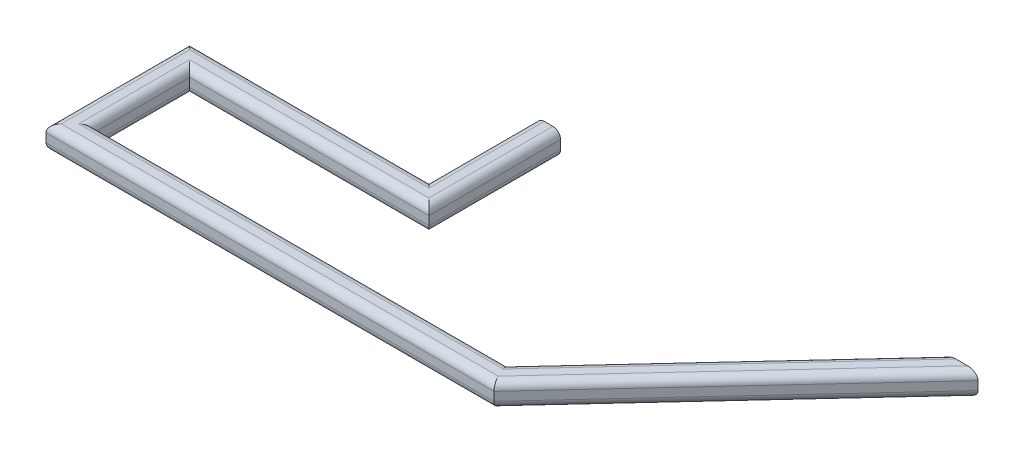
SolidWorks part; units mm, degrees
ref_plane "Front Plane" through (0, 0, 0) normal (0, 0, 1) x (1, 0, 0)
ref_plane "Top Plane" through (0, 0, 0) normal (0, 1, 0) x (1, 0, 0)
ref_plane "Right Plane" through (0, 0, 0) normal (1, 0, 0) x (0, 0, -1)
sketch "Sketch2" plane through (0, 0, 0) normal (0, 1, 0) x (1, 0, 0)
  line L1 (0, 0) -> (200, 0)
  line L2 (200, 0) -> (431.5, 250)
  line L3 (431.5, 250) -> (439.993, 259.1717)
  line L4 (439.993, 259.1717) -> (448.8318, 250.3328) construction
  line L5 (448.8318, 250.3328) -> (431.1541, 268.0105) construction
  line L6 (0, 125) -> (-250, 125)
  line L7 (-250, 125) -> (-250, 0)
  line L8 (-250, 0) -> (0, 0)
  line L9 (0, 250) -> (0, 125)
  point P4 (439.993, 259.1717)
  dimension "D1" = 250
  dimension "D2" = 431.5
  dimension "D3" = 200
  dimension "D4" = 12.5
  dimension "D5" = 25
  dimension "D6" = 250
  dimension "D7" = 125
ref_plane "Plane1" through (0, 0, -250) normal (0, 0, 1) x (1, 0, 0)
sketch "Sketch6" plane through (0, 0, -250) normal (0, 0, 1) x (1, 0, 0)
  line L1 (-4.5, -9.5) -> (4.5, -9.5)
  line L2 (-9.5, -4.5) -> (-9.5, 4.5)
  line L3 (-4.5, 9.5) -> (4.5, 9.5)
  line L4 (9.5, -4.5) -> (9.5, 4.5)
  line L5 (-9.5, -9.5) -> (9.5, 9.5) construction
  line L6 (-9.5, 9.5) -> (9.5, -9.5) construction
  arc A0 (9.5, -4.5) -> (4.5, -9.5) centre (4.5, -4.5) cw
  arc A1 (-4.5, -9.5) -> (-9.5, -4.5) centre (-4.5, -4.5) cw
  arc A2 (-9.5, 4.5) -> (-4.5, 9.5) centre (-4.5, 4.5) cw
  arc A3 (4.5, 9.5) -> (9.5, 4.5) centre (4.5, 4.5) cw
  point P0 (0, 0)
  dimension "D3" = 5
  dimension "D1" = 19
  dimension "D2" = 19
sweep "Sweep-Thin1" add profiles "Sketch6" path "Sketch2" parameters "D1"=3
sketch "Sketch11" plane through (0, 0, -250) normal (0, 0, 1) x (1, 0, 0)
  line L1 (319.6496, 28.5569) -> (454.9899, 28.5569)
  line L2 (319.6496, 28.5569) -> (319.6496, -28.5569)
  line L3 (319.6496, -28.5569) -> (454.9899, -28.5569)
  line L4 (454.9899, 28.5569) -> (454.9899, -28.5569)
  line L5 (319.6496, 28.5569) -> (454.9899, -28.5569) construction
  line L6 (319.6496, -28.5569) -> (454.9899, 28.5569) construction
  point P0 (387.3198, 0)
extrude "Cut-Extrude1" cut sketch "Sketch11" against normal through all
ref_plane "Plane2" through (0, -22.5, 0) normal (0, -1, 0) x (-1, 0, 0)
sketch "Sketch12" plane through (0, -22.5, 0) normal (0, -1, 0) x (-1, 0, 0)
  line L0 (0, 0) -> (160, 0) construction
  line L1 (160, 0) -> (160, -55.5646) construction
  dimension "D1" = 160
